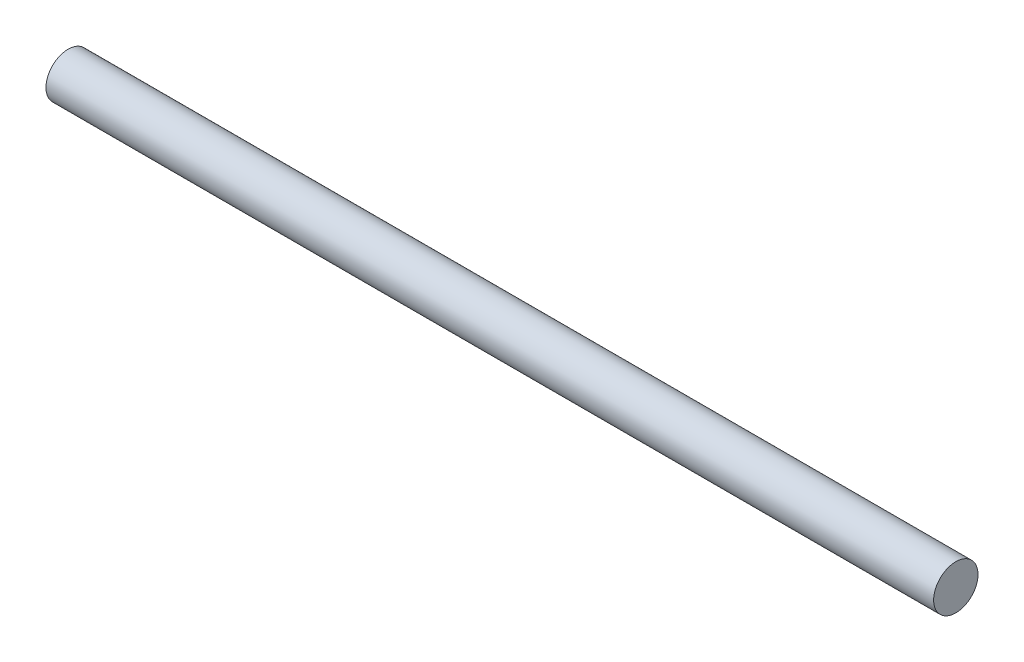
SolidWorks part; units mm, degrees
ref_plane "Front Plane" through (0, 0, 0) normal (0, 0, 1) x (1, 0, 0)
ref_plane "Top Plane" through (0, 0, 0) normal (0, 1, 0) x (1, 0, 0)
ref_plane "Right Plane" through (0, 0, 0) normal (1, 0, 0) x (0, 0, -1)
sketch "Sketch1" plane through (0, 0, 0) normal (1, 0, 0) x (0, 0, -1)
  circle A0 centre (0, 0) radius 2
  dimension "D1" = 4
extrude "Boss-Extrude1" add sketch "Sketch1" along normal mid plane 80
